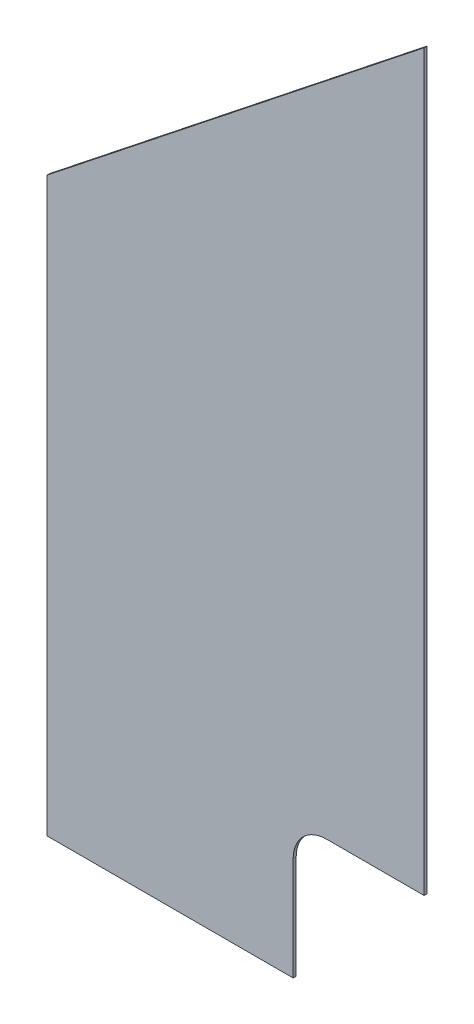
SolidWorks part; units mm, degrees
material "PC High Viscosity"
ref_plane "Front Plane" through (0, 0, 0) normal (0, 0, 1) x (1, 0, 0)
ref_plane "Top Plane" through (0, 0, 0) normal (0, 1, 0) x (1, 0, 0)
ref_plane "Right Plane" through (0, 0, 0) normal (1, 0, 0) x (0, 0, -1)
sketch "Sketch1" plane through (0, 0, 0) normal (0, 0, 1) x (1, 0, 0)
  line L0 (0, 0) -> (-393.7, 0)
  line L1 (-393.7, 0) -> (-393.7, 596.9)
  line L2 (-393.7, 596.9) -> (0, 908.9428)
  line L4 (0, 908.9428) -> (0, 0)
  dimension "D1" = 596.9
  dimension "D2" = 128.4
  dimension "D4" = 393.7
extrude "Boss-Extrude1" add sketch "Sketch1" along normal blind 3.175
sketch "Sketch2" plane through (0, 0, 3.175) normal (0, 0, 1) x (1, 0, 0)
  line L0 (-393.7, 0) -> (0, 0) construction
  line L1 (-114.3, 101.6) -> (-88.9, 101.6)
  line L2 (-114.3, 101.6) -> (-114.3, 0)
  line L3 (-114.3, 0) -> (-88.9, 0)
  line L4 (-88.9, 101.6) -> (-88.9, 0)
  line L5 (-114.3, 101.6) -> (-88.9, 0) construction
  line L6 (-114.3, 0) -> (-88.9, 101.6) construction
  line L8 (-101.6, 101.6) -> (-101.6, 0) construction
  line L10 (-393.7, 596.9) -> (-393.7, 0) construction
  point P0 (-101.6, 50.8)
  dimension "D1" = 25.4
  dimension "D2" = 292.1
  dimension "D3" = 101.6
extrude "Cut-Extrude1" [suppressed] cut sketch "Sketch2" against normal through all
fillet "Fillet1" [suppressed] radius 12.7
sketch "Sketch3" plane through (0, 0, 3.175) normal (0, 0, 1) x (1, 0, 0)
  line L1 (-400.05, 85.852) -> (-387.35, 85.852)
  line L2 (-400.05, 85.852) -> (-400.05, 66.802)
  line L3 (-400.05, 66.802) -> (-387.35, 66.802)
  line L4 (-381, 79.502) -> (-381, 73.152)
  line L8 (-393.7, 563.4463) -> (-384.175, 563.4463)
  line L9 (-371.475, 576.1463) -> (-371.475, 614.5153)
  line L10 (-371.475, 614.5153) -> (-393.7, 596.9)
  line L11 (-393.7, 596.9) -> (-393.7, 0) construction
  line L12 (-393.7, 596.9) -> (-393.7, 563.4463)
  line L13 (0, 908.9428) -> (-393.7, 596.9) construction
  arc A0 (-387.35, 85.852) -> (-381, 79.502) centre (-387.35, 79.502) cw
  arc A1 (-387.35, 66.802) -> (-381, 73.152) centre (-387.35, 73.152) ccw
  arc A3 (-384.175, 563.4463) -> (-371.475, 576.1463) centre (-384.175, 576.1463) ccw
  dimension "D1" = 6.35
  dimension "D5" = 12.7
  dimension "D2" = 12.7
  dimension "D3" = 19.05
  dimension "D4" = 22.225
  dimension "D6" = 33.4537
extrude "Cut-Extrude2" [suppressed] cut sketch "Sketch3" against normal through all
sketch "Sketch4" plane through (0, 0, 3.175) normal (0, 0, 1) x (1, 0, 0)
  line L7 (0, 0) -> (-136.652, 0)
  line L8 (0, 0) -> (0, 142.875)
  line L9 (0, 142.875) -> (-101.727, 142.875)
  line L10 (-136.652, 0) -> (-136.652, 107.95)
  arc A0 (-101.727, 142.875) -> (-136.652, 107.95) centre (-101.727, 107.95) ccw
  point P7 (-136.652, 142.875)
  dimension "D3" = 34.925
  dimension "D1" = 142.875
  dimension "D2" = 136.652
extrude "Cut-Extrude3" cut sketch "Sketch4" against normal through all
